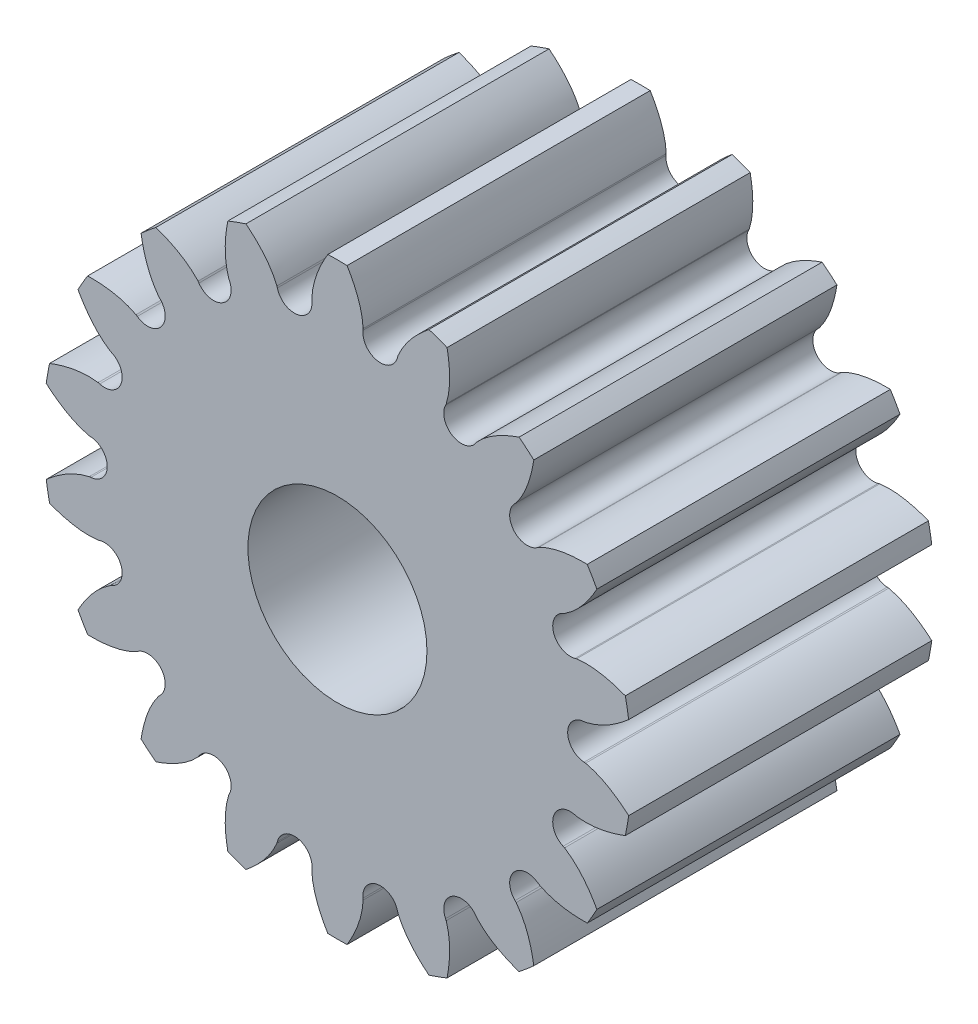
SolidWorks part; units mm, degrees
material "PE Low/Medium Density"
ref_plane "Front Plane" through (0, 0, 0) normal (0, 0, 1) x (1, 0, 0)
ref_plane "Top Plane" through (0, 0, 0) normal (0, 1, 0) x (1, 0, 0)
ref_plane "Right Plane" through (0, 0, 0) normal (1, 0, 0) x (0, 0, -1)
sketch "Involute construction sketch" plane through (0, 0, 0) normal (0, 0, 1) x (1, 0, 0)
  line L0 (0, 0) -> (-1.8157, 1.6751) construction
  line L1 (0, 0) -> (-1.2188, 2.1487) construction
  line L2 (0, 0) -> (-0.506, 2.418) construction
  line L3 (0, 0) -> (0.255, 2.4572) construction
  line L4 (-2.4509, 0.3098) -> (-2.2398, 1.042) construction
  line L5 (-2.2398, 1.042) -> (-1.8157, 1.6751) construction
  line L6 (-1.8157, 1.6751) -> (-1.2188, 2.1487) construction
  line L7 (0, 0) -> (-2.2398, 1.042) construction
  line L8 (0, 0) -> (-2.4509, 0.3098) construction
  line L9 (-1.2188, 2.1487) -> (-0.506, 2.418) construction
  line L10 (-0.506, 2.418) -> (0.255, 2.4572) construction
  line L11 (-2.4509, 0.3098) -> (-1.9731, 4.0897) construction
  line L12 (-2.2398, 1.042) -> (-0.9542, 3.8056) construction
  line L13 (-1.8157, 1.6751) -> (-0.2657, 3.3553) construction
  line L14 (-1.2188, 2.1487) -> (0.1068, 2.9007) construction
  line L15 (-0.506, 2.418) -> (0.2399, 2.5741) construction
  line L17 (0, 0) -> (0, 5.7859) construction
  line L18 (0, 0) -> (0.2291, 2.6189) construction
  line L19 (0, 0) -> (0.397, 2.2513) construction
  circle A0 centre (0, 0) radius 2.286 construction
  circle A1 centre (0, 0) radius 2.4704 construction
  circle A2 centre (0, 0) radius 2.6289 construction
  circle A3 centre (0, 0) radius 2.921 construction
  spline S0 degree 3 poles (0.255, 2.4572) (0.2476, 2.615) (0.11, 2.9502) (-0.5314, 3.7068) (-1.3595, 4.0133) (-1.9731, 4.0897) knots 0 0 0 0 0.160126 0.360107 1 1 1 1 construction
  point P17 (0.0957, 2.9194)
  dimension "D1" = 4.572
  dimension "D2" = 4.9407
  dimension "D3" = 5.2578
  dimension "D4" = 5.842
  dimension "D5" = 0.762
  dimension "D6" = 1.524
  dimension "D7" = 2.286
  dimension "D8" = 3.048
  dimension "D9" = 3.81
  dimension "D10" = 5
  dimension "D11" = 10
sketch "Sketch2" plane through (0, 0, 0) normal (0, 0, 1) x (1, 0, 0)
  line L0 (0, 2.921) -> (0, 2.286)
  line L1 (0, 0) -> (0, 5.7859) construction
  line L2 (0.255, 2.4572) -> (0.2534, 2.4415)
  line L3 (0, 0) -> (0.255, 2.4572) construction
  circle A0 centre (0, 0) radius 2.921 construction
  circle A1 centre (0, 0) radius 2.286 construction
  arc A2 (0, 2.921) -> (0.0957, 2.9194) centre (0, 0) cw
  arc A3 (0, 2.286) -> (0.397, 2.2513) centre (0, 0) cw
  arc A4 (0.2534, 2.4415) -> (0.397, 2.2513) centre (0.4273, 2.4235) ccw
  spline S0 degree 3 poles (0.255, 2.4572) (0.2525, 2.512) (0.2249, 2.6747) (0.152, 2.8255) (0.0957, 2.9194) knots 0 0 0 0 0.332628 1 1 1 1
sketch "Sketch3" plane through (0, 0, 0) normal (0, 0, 1) x (1, 0, 0)
  circle A0 centre (0, 0) radius 2.286
  circle A1 centre (0, 0) radius 0.889
  dimension "D1" = 4.572
  dimension "D2" = 1.778
extrude "Base" add sketch "Sketch3" along normal blind 3.0099
extrude "Half tooth" add sketch "Sketch2" along normal up to surface (3.0099 mm away) up to face at (2.286, 0, 3.0099)
ref_plane "Midplane of half tooth" through (0, 0, 0) normal (-1, 0, 0) x (0, 0, 1)
mirror "Mirror of half tooth" about plane through (0, 0, 0) normal (-1, 0, 0) of "Half tooth"
pattern_circular "Pattern of tooth" count 18 over 360 about axis through (0, 0, 3.0099) along (0, 0, 1) of "Half tooth", "Mirror of half tooth"
equation "\"radtodeg\"= 180 / PI'radian to degree conversion [ ]"
equation "\"phi\"= 20'pressure angle [deg]"
equation "\"N\"= 18'number of teeth [teeth]"
equation "\"A\"= 0.230in'diameter of addendum circle [inch]"
equation "\"B\"= 0.18in'diameter of dedendum circle [inch]"
equation "\"P\"= ( \"N\" + 2 ) / \"A\"'diametral pitch [teeth/inch]"
equation "\"d\"= \"N\" / \"P\"'diameter of pitch circle [inch]"
equation "\"cp\"= PI / \"P\"'circular pitch [inch/teeth]"
equation "\"add\"= 1 / \"P\"'addendum [inch]"
equation "\"ded\"= - ( \"B\" - \"d\" ) / 2'dedendum [inch]"
equation "\"clear\"= \"ded\" - \"add\"'clearance [inch]"
equation "\"C\"= \"B\" + 2 * \"clear\"'diameter of clearance circle [inch]"
equation "\"h\"= \"add\" + \"ded\"'tooth height / whole depth [inch]"
equation "\"s\"= \"d\" * cos ( \"phi\" * 1 / \"radtodeg\" )'diameter of base circle [inch]"
equation "\"t\"= ( PI / 2 ) / \"P\"'tooth width at diameter of pitch circle diameter [inch]"
equation "\"alpha\"= ( \"t\" / ( \"d\" / 2 ) * \"radtodeg\" ) / 2'arc angle for half of tooth width at pitch circle diameter [inch]"
equation "\"bore\"= 0.07'bore of hub [inch]"
equation "\"D4@Involute construction sketch\"= \"A\"'addendum circle"
equation "\"D3@Involute construction sketch\"= \"d\"'pitch circle"
equation "\"D2@Involute construction sketch\"= \"s\"'base circle"
equation "\"D1@Involute construction sketch\"= \"B\"'dedendum circle"
equation "\"seg\"= \"D5@Involute construction sketch\"'size of one involute segment [inch]"
equation "\"D6@Involute construction sketch\"=2*\"seg\""
equation "\"D7@Involute construction sketch\"=3*\"seg\""
equation "\"D8@Involute construction sketch\"=4*\"seg\""
equation "\"D9@Involute construction sketch\"=5*\"seg\""
equation "\"D10@Involute construction sketch\"=\"alpha\""
equation "\"D11@Involute construction sketch\"=2*\"alpha\""
equation "\"D1@Sketch3\"=\"B\""
equation "\"D2@Sketch3\"=\"bore\""
